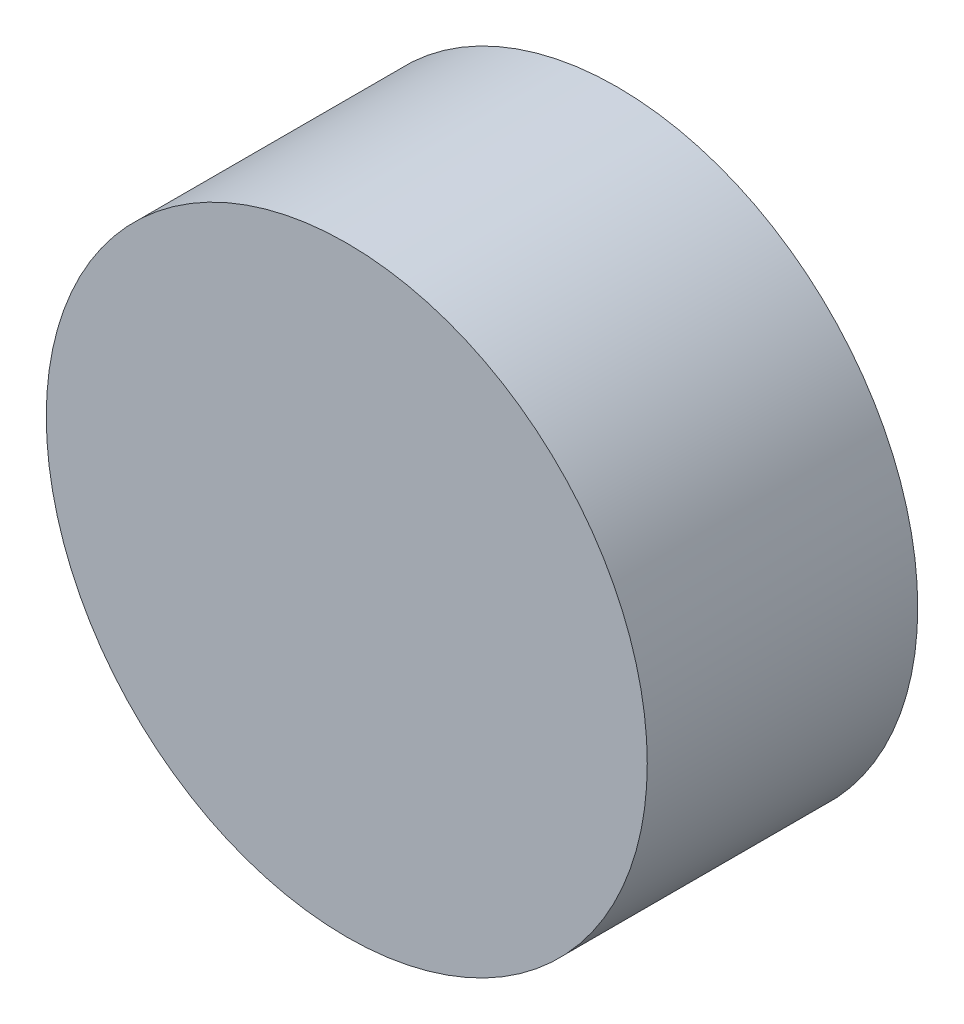
SolidWorks part; units mm, degrees
ref_plane "Front Plane" through (0, 0, 0) normal (0, 0, 1) x (1, 0, 0)
ref_plane "Top Plane" through (0, 0, 0) normal (0, 1, 0) x (1, 0, 0)
ref_plane "Right Plane" through (0, 0, 0) normal (1, 0, 0) x (0, 0, -1)
sketch "Sketch1" plane through (0, 0, 0) normal (0, 0, 1) x (1, 0, 0)
  line L0 (25, -171.8) -> (25, 142.2564) construction
  line L1 (-37.94, -240.332) -> (139.86, -240.332) construction
  circle A0 centre (0, -151.01) radius 10
  dimension "D1" = 20
  dimension "D2" = 25
  dimension "D3" = 89.322
extrude "Boss-Extrude1" add sketch "Sketch1" along normal blind 9 contours A0
